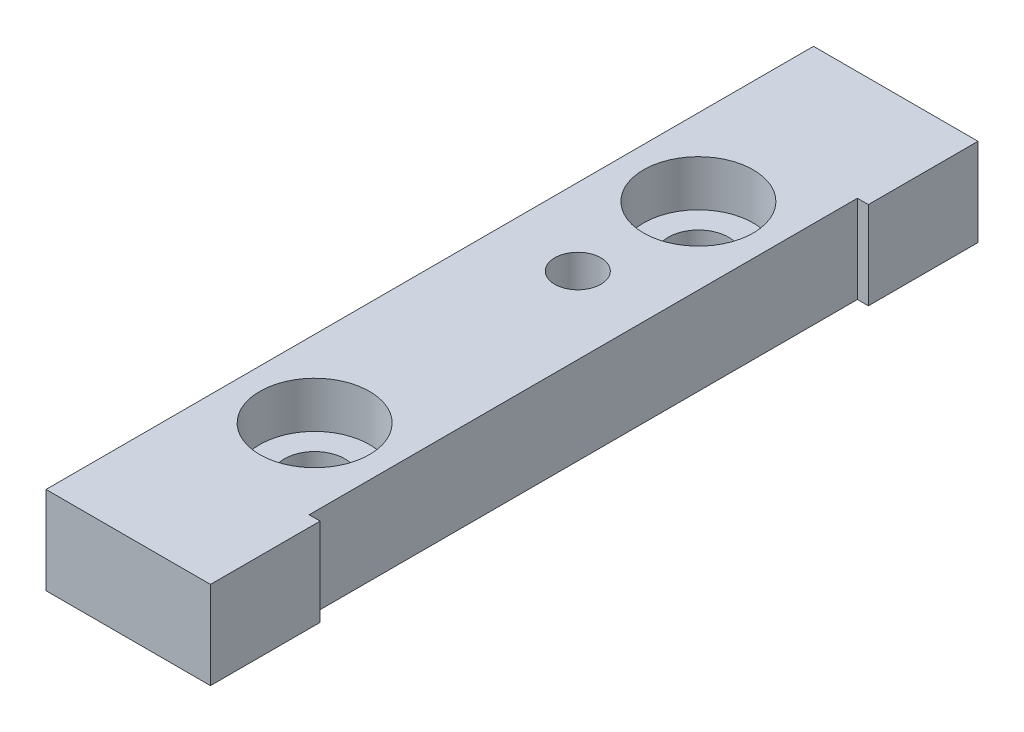
SolidWorks part; units mm, degrees
ref_plane "Front Plane" through (0, 0, 0) normal (0, 0, 1) x (1, 0, 0)
ref_plane "Top Plane" through (0, 0, 0) normal (0, 1, 0) x (1, 0, 0)
ref_plane "Right Plane" through (0, 0, 0) normal (1, 0, 0) x (0, 0, -1)
sketch "Sketch1" plane through (0, 0, 0) normal (0, 1, 0) x (1, 0, 0)
  line L0 (7.5, 25) -> (6.5, 25)
  line L1 (-7.5, -35) -> (7.5, -35)
  line L2 (-7.5, -35) -> (-7.5, 35)
  line L3 (-7.5, 35) -> (7.5, 35)
  line L4 (7.5, -35) -> (7.5, -25)
  line L5 (-7.5, -35) -> (7.5, 35) construction
  line L6 (-7.5, 35) -> (7.5, -35) construction
  line L7 (6.5, 25) -> (6.5, -25)
  line L8 (6.5, -25) -> (7.5, -25)
  line L9 (7.5, 25) -> (7.5, 35)
  point P0 (0, 0)
  dimension "D1" = 15
  dimension "D2" = 70
  dimension "D3" = 10
  dimension "D4" = 10
  dimension "D5" = 1
extrude "Boss-Extrude1" add sketch "Sketch1" along normal blind 8
sketch "Sketch2" plane through (0, 8, 0) normal (0, 1, 0) x (1, 0, 0)
  line L0 (-7.5, 35) -> (-7.5, -35) construction
  circle A0 centre (-0.5, 17.5) radius 2.75
  circle A1 centre (-0.5, -17.5) radius 2.75
  dimension "D1" = 5.5
  dimension "D2" = 5.5
  dimension "D3" = 17.5
  dimension "D4" = 17.5
  dimension "D5" = 7
  dimension "D6" = 7
extrude "Cut-Extrude1" cut sketch "Sketch2" against normal through all contours A1 | A0
sketch "Sketch3" plane through (0, 8, 0) normal (0, 1, 0) x (1, 0, 0)
  circle A0 centre (-0.5, 17.5) radius 5
  circle A1 centre (-0.5, -17.5) radius 5
extrude "Cut-Extrude2" cut sketch "Sketch3" against normal blind 4.2
hole_wizard "M5 Tapped Hole1" positions "Sketch4" profile "Sketch5" tap size "M5" standard "DIN" end condition through all
sketch "Sketch4" plane through (0, 8, 0) normal (0, 1, 0) x (1, 0, 0)
  line L0 (-7.5, 35) -> (-7.5, -35) construction
  line L1 (-7.5, -35) -> (7.5, -35) construction
  point P0 (-0.5, 6.5)
  dimension "D1" = 7
  dimension "D2" = 41.5
sketch "Sketch5" plane through (-0.5, 8, -6.5) normal (1, 0, 0) x (0, 0, 1)
  line L0 (0, 0) -> (0, 8)
  line L1 (0, 8) -> (2.1, 8)
  line L2 (2.1, 8) -> (2.1, 0)
  line L5 (2.1, 0) -> (0, 0)
  line L11 (0, -6.35) -> (0, 107.95) construction
  dimension "Thru Tap Drill Dia." = 4.2
  dimension "Thru Tap Drill Depth" = 8
cosmetic thread "Hole Thread1" parameters "D2"=5
